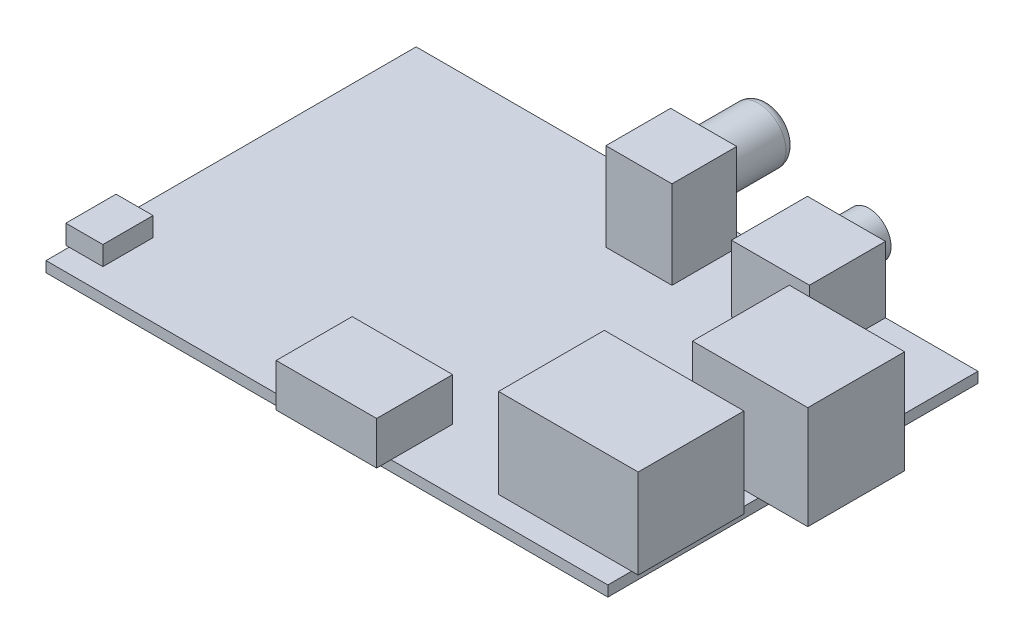
SolidWorks part; units mm, degrees
ref_plane "Front Plane" through (0, 0, 0) normal (0, 0, 1) x (1, 0, 0)
ref_plane "Top Plane" through (0, 0, 0) normal (0, 1, 0) x (1, 0, 0)
ref_plane "Right Plane" through (0, 0, 0) normal (1, 0, 0) x (0, 0, -1)
sketch "Sketch1" plane through (0, 0, 0) normal (0, 1, 0) x (1, 0, 0)
  line L1 (42.5, -28) -> (-42.5, -28)
  line L2 (42.5, -28) -> (42.5, 28)
  line L3 (42.5, 28) -> (-42.5, 28)
  line L4 (-42.5, -28) -> (-42.5, 28)
  line L5 (42.5, -28) -> (-42.5, 28) construction
  line L6 (42.5, 28) -> (-42.5, -28) construction
  point P0 (0, 0)
  dimension "D1" = 56
  dimension "D2" = 85
extrude "Boss-Extrude1" add sketch "Sketch1" along normal blind 1.6
sketch "Sketch5" plane through (0, 1.6, 0) normal (0, 1, 0) x (1, 0, 0)
  line L0 (-42.5, 28) -> (-42.5, -28) construction
  line L1 (-43, -16.9) -> (-37.4, -16.9)
  line L2 (-43, -16.9) -> (-43, -24.5)
  line L3 (-43, -24.5) -> (-37.4, -24.5)
  line L4 (-37.4, -16.9) -> (-37.4, -24.5)
  line L5 (-42.5, -28) -> (42.5, -28) construction
  dimension "D1" = 0.5
  dimension "D2" = 3.5
  dimension "D3" = 5.6
  dimension "D4" = 7.6
extrude "Boss-Extrude4" add sketch "Sketch5" along normal blind 2.9
sketch "Sketch7" plane through (0, 1.6, 0) normal (0, 1, 0) x (1, 0, 0)
  line L0 (-42.5, -24.5) -> (-42.5, -28) construction
  line L1 (-5.5, -18.6787) -> (9.7, -18.6787)
  line L2 (-5.5, -18.6787) -> (-5.5, -30.1787)
  line L3 (-5.5, -30.1787) -> (9.7, -30.1787)
  line L4 (9.7, -18.6787) -> (9.7, -30.1787)
  dimension "D1" = 37
  dimension "D2" = 11.5
  dimension "D3" = 15.2
extrude "Boss-Extrude5" add sketch "Sketch7" along normal blind 6.5
sketch "Sketch8" plane through (0, 1.6, 0) normal (0, 1, 0) x (1, 0, 0)
  line L0 (42.5, -28) -> (42.5, 28) construction
  line L1 (22.38, -24.4098) -> (43.5, -24.4098)
  line L2 (22.38, -24.4098) -> (22.38, -8.4098)
  line L3 (22.38, -8.4098) -> (43.5, -8.4098)
  line L4 (43.5, -24.4098) -> (43.5, -8.4098)
  dimension "D1" = 1
  dimension "D2" = 16
  dimension "D3" = 21.12
extrude "Boss-Extrude6" add sketch "Sketch8" along normal blind 13.5
sketch "Sketch9" plane through (0, 1.6, 0) normal (0, 1, 0) x (1, 0, 0)
  line L0 (42.5, -8.4098) -> (42.5, 28) construction
  line L1 (32.55, 9.4) -> (50, 9.4)
  line L2 (32.55, 9.4) -> (32.55, -5.25)
  line L3 (32.55, -5.25) -> (50, -5.25)
  line L4 (50, 9.4) -> (50, -5.25)
  line L5 (42.5, 28) -> (-42.5, 28) construction
  dimension "D1" = 14.65
  dimension "D2" = 17.45
  dimension "D3" = 7.5
  dimension "D4" = 18.6
extrude "Boss-Extrude7" add sketch "Sketch9" along normal blind 15.6
sketch "Sketch10" plane through (0, 1.6, 0) normal (0, 1, 0) x (1, 0, 0)
  line L0 (42.5, 28) -> (-42.5, 28) construction
  line L1 (16.7, 28) -> (28.5, 28)
  line L2 (16.7, 28) -> (16.7, 16.5)
  line L3 (16.7, 16.5) -> (28.5, 16.5)
  line L4 (28.5, 28) -> (28.5, 16.5)
  line L5 (42.5, 9.4) -> (42.5, 28) construction
  dimension "D1" = 14
  dimension "D2" = 11.8
  dimension "D3" = 11.5
extrude "Boss-Extrude8" add sketch "Sketch10" along normal blind 10.02
sketch "Sketch11" plane through (0, 0, -28) normal (0, 0, -1) x (-1, 0, 0)
  line L0 (-42.5, 1.6) -> (-22.38, 1.6) construction
  line L1 (-29.7025, 1.6) -> (-13.5443, 1.6) construction
  line L2 (-16.7, 1.6) -> (42.5, 1.6) construction
  line L3 (-18.0569, 4.6) -> (-27.2278, 4.6) construction
  line L4 (-16.7, 11.62) -> (-28.5, 11.62) construction
  line L5 (-28.5, 11.62) -> (-22.6, 11.62) construction
  line L6 (-22.6, 11.62) -> (-22.6, -2.8272) construction
  circle A0 centre (-22.6, 7.95) radius 3.35
  dimension "D1" = 6.7
  dimension "D2" = 3
extrude "Boss-Extrude9" add sketch "Sketch11" along normal blind 3.4
sketch "Sketch12" plane through (0, 1.6, 0) normal (0, 1, 0) x (1, 0, 0)
  line L0 (16.7, 28) -> (-42.5, 28) construction
  line L1 (8.1, 16.1) -> (-1.9, 16.1)
  line L2 (8.1, 16.1) -> (8.1, 25.9)
  line L3 (8.1, 25.9) -> (-1.9, 25.9)
  line L4 (-1.9, 16.1) -> (-1.9, 25.9)
  line L5 (-42.5, 28) -> (-42.5, -16.9) construction
  dimension "D1" = 10
  dimension "D2" = 9.8
  dimension "D3" = 2.1
  dimension "D4" = 40.6
extrude "Boss-Extrude10" add sketch "Sketch12" along normal blind 13.3
sketch "Sketch14" plane through (0, 0, -25.9) normal (0, 0, -1) x (-1, 0, 0)
  line L0 (-8.1, 14.9) -> (1.9, 14.9) construction
  line L1 (1.9, 14.9) -> (-3.1, 14.9) construction
  line L2 (-3.1, 14.9) -> (-3.1, 5.7793) construction
  line L3 (-3.1, 5.6) -> (1.05, 5.6) construction
  line L4 (1.05, 5.6) -> (-7.0539, 5.6) construction
  line L5 (-7.6002, 1.6) -> (1.05, 1.6) construction
  line L6 (-8.1, 1.6) -> (1.9, 1.6) construction
  line L7 (-16.7, 1.6) -> (42.5, 1.6) construction
  circle A0 centre (-3.1, 9.75) radius 4.15
  dimension "D1" = 8.3
  dimension "D2" = 4
extrude "Boss-Extrude11" add sketch "Sketch14" along normal blind 9.8
sketch "Sketch15" plane through (0, 0, 0) normal (0, -1, 0) x (1, 0, 0)
  line L0 (42.5, -28) -> (-42.5, -28) construction
  line L1 (-41.5, 13.5) -> (-22.5, 13.5)
  line L2 (-41.5, 13.5) -> (-41.5, -16.5)
  line L3 (-41.5, -16.5) -> (-22.5, -16.5)
  line L4 (-22.5, 13.5) -> (-22.5, -16.5)
  line L6 (-42.5, -28) -> (-42.5, 28) construction
  dimension "D1" = 30
  dimension "D2" = 19
  dimension "D3" = 11.5
  dimension "D4" = 1
extrude "Boss-Extrude12" add sketch "Sketch15" along normal blind 5
sketch "Sketch16" plane through (0, 0, -35.7) normal (0, 0, -1) x (-1, 0, 0)
  line L0 (-3.1, 13.9) -> (-3.1, 5.6) construction
  circle A0 centre (-3.1, 9.75) radius 4.15 construction
  circle A1 centre (-3.1, 9.75) radius 2.25
  dimension "D1" = 4.5
extrude "Cut-Extrude1" cut sketch "Sketch16" against normal blind 8
fillet "Fillet1" radius 1.5 1 edges at (-1.05, 9.75, -35.7)
sketch "Sketch17" plane through (0, 0, -31.4) normal (0, 0, -1) x (-1, 0, 0)
  line L0 (-22.6, 11.3) -> (-22.6, 4.6) construction
  circle A0 centre (-22.6, 7.95) radius 3.35 construction
  circle A1 centre (-22.6, 7.95) radius 1.775
  dimension "D1" = 3.55
extrude "Cut-Extrude2" cut sketch "Sketch17" against normal blind 8
fillet "Fillet2" radius 0.25 1 edges at (20.825, 7.95, -31.4)
